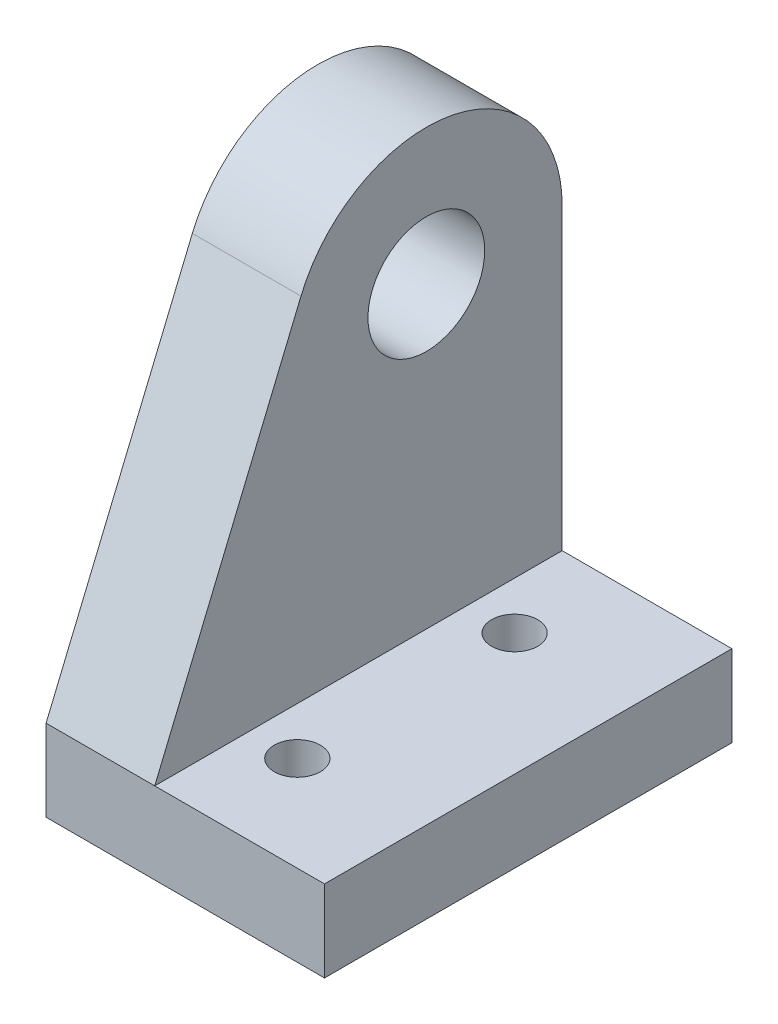
SolidWorks part; units mm, degrees
material "ABS"
ref_plane "Front" through (0, 0, 0) normal (0, 0, 1) x (1, 0, 0)
ref_plane "Top" through (0, 0, 0) normal (0, 1, 0) x (1, 0, 0)
ref_plane "Right" through (0, 0, 0) normal (1, 0, 0) x (0, 0, -1)
sketch "Croquis1" plane through (0, 0, 0) normal (0, 0, 1) x (1, 0, 0)
  line L0 (0, 0) -> (-12.5, 0)
  line L1 (-12.5, 0) -> (-12.5, 32)
  line L2 (-12.5, 32) -> (-20.5, 32)
  line L3 (-20.5, 32) -> (-20.5, -6)
  line L4 (-20.5, -6) -> (0, -6)
  line L5 (0, 0) -> (0, 9.8876) construction
  line L6 (0, 0) -> (0, -6)
  dimension "D1" = 25
  dimension "D2" = 6
  dimension "D3" = 8
  dimension "D4" = 32
extrude "Saliente-Extruir1" add sketch "Croquis1" along normal blind 30
sketch "Croquis2" plane through (-20.5, 0, 0) normal (-1, 0, 0) x (0, 0, 1)
  line L0 (30, 0) -> (19.2308, 25.8462)
  line L1 (0, 32) -> (0, -6) construction
  line L2 (30, 32) -> (0, 32) construction
  line L3 (0, 22) -> (0, 21)
  line L4 (0, 21) -> (-1, 21)
  line L5 (-1, 21) -> (-1, 33)
  line L6 (-1, 33) -> (31, 33)
  line L7 (30, 0) -> (31, 0)
  line L8 (31, 0) -> (31, 33)
  line L9 (30, 32) -> (30, -6) construction
  arc A0 (19.2308, 25.8462) -> (0, 22) centre (10, 22) ccw
  circle A1 centre (10, 22) radius 4.3
  dimension "D4" = 8.6
  dimension "D5" = 10
  dimension "D1" = 1
  dimension "D2" = 1
  dimension "D3" = 1
extrude "Cortar-Extruir1" cut sketch "Croquis2" against normal through all
sketch "Croquis3" plane through (0, -6, 0) normal (0, -1, 0) x (1, 0, 0)
  line L0 (0, 30) -> (0, 0) construction
  line L1 (9, 7) -> (-9, 7) construction
  line L2 (9, 7) -> (9, 23) construction
  line L3 (9, 23) -> (-9, 23) construction
  line L4 (-9, 7) -> (-9, 23) construction
  line L5 (9, 7) -> (-9, 23) construction
  line L6 (9, 23) -> (-9, 7) construction
  circle A0 centre (-9, 23) radius 1.7
  circle A1 centre (-9, 7) radius 1.7
  point P0 (0, 15)
  dimension "D1" = 3.4
  dimension "D2" = 16
  dimension "D3" = 18
extrude "Cortar-Extruir2" cut sketch "Croquis3" against normal up to next
